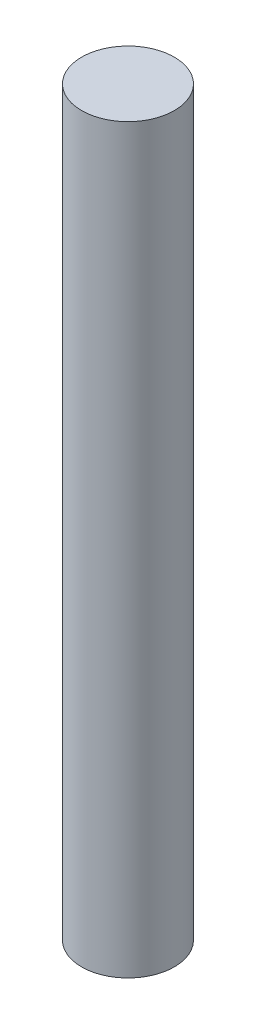
SolidWorks part; units mm, degrees
ref_plane "Front Plane" through (0, 0, 0) normal (0, 0, 1) x (1, 0, 0)
ref_plane "Top Plane" through (0, 0, 0) normal (0, 1, 0) x (1, 0, 0)
ref_plane "Right Plane" through (0, 0, 0) normal (1, 0, 0) x (0, 0, -1)
sketch "Sketch1" plane through (0, 0, 0) normal (0, 1, 0) x (1, 0, 0)
  circle A0 centre (0, 0) radius 2
  dimension "D1" = 4
extrude "Boss-Extrude1" add sketch "Sketch1" along normal blind 32
